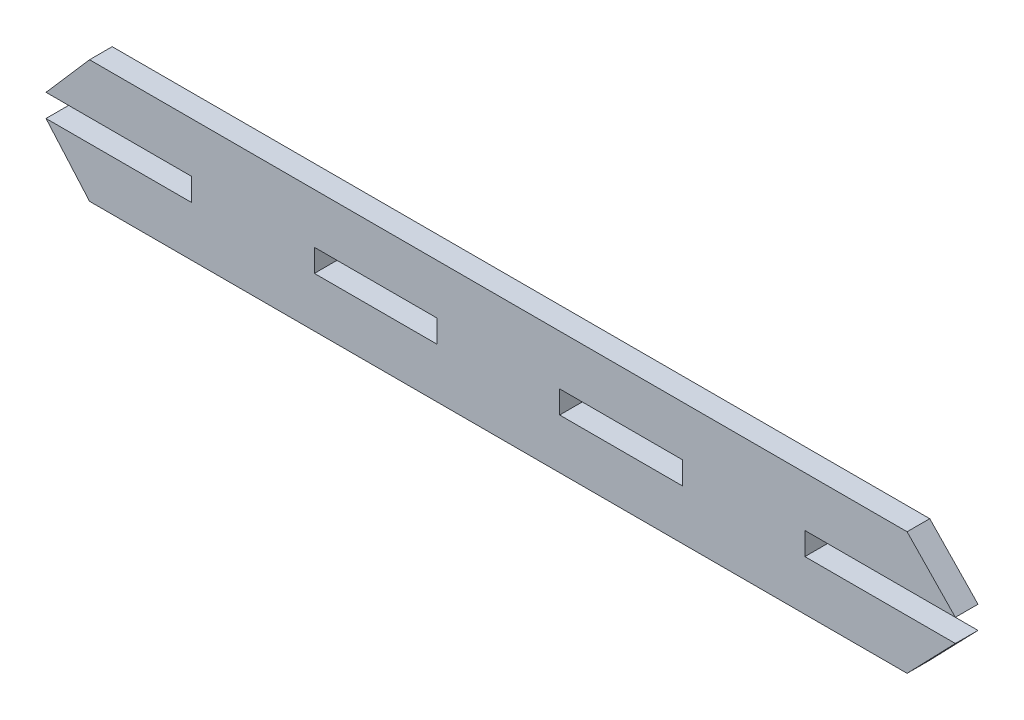
SolidWorks part; units mm, degrees
ref_plane "Front Plane" through (0, 0, 0) normal (0, 0, 1) x (1, 0, 0)
ref_plane "Top Plane" through (0, 0, 0) normal (0, 1, 0) x (1, 0, 0)
ref_plane "Right Plane" through (0, 0, 0) normal (1, 0, 0) x (0, 0, -1)
sketch "Sketch2" plane through (0, 0, 0) normal (0, 0, 1) x (1, 0, 0)
  line L5 (70.8837, 21.3653) -> (270.8837, 21.3653)
  line L35 (170.8837, 21.3653) -> (170.8837, 6.3653) construction
  line L40 (70.8837, -8.6347) -> (270.8837, -8.6347)
  line L42 (185.8837, 9.1353) -> (215.8837, 9.1353)
  line L43 (185.8837, 9.1353) -> (185.8837, 3.5953)
  line L44 (185.8837, 3.5953) -> (215.8837, 3.5953)
  line L45 (215.8837, 9.1353) -> (215.8837, 3.5953)
  line L57 (60.2283, 9.1353) -> (70.8837, 21.3653)
  line L58 (60.2283, 3.5953) -> (70.8837, -8.6347)
  line L59 (270.8837, -8.6347) -> (282.6872, 3.5953)
  line L60 (270.8837, 21.3653) -> (282.6872, 9.1353)
  line L62 (125.8837, 9.1353) -> (125.8837, 3.5953)
  line L63 (125.8837, 9.1353) -> (155.8837, 9.1353)
  line L64 (155.8837, 9.1353) -> (155.8837, 3.5953)
  line L65 (125.8837, 3.5953) -> (155.8837, 3.5953)
  line L67 (60.2283, 3.5953) -> (95.8837, 3.5953)
  line L69 (60.2283, 9.1353) -> (95.8837, 9.1353)
  line L70 (95.8837, 3.5953) -> (95.8837, 9.1353)
  line L71 (282.6872, 3.5953) -> (245.8837, 3.5953)
  line L73 (282.6872, 9.1353) -> (245.8837, 9.1353)
  line L74 (245.8837, 3.5953) -> (245.8837, 9.1353)
  point P12 (170.8837, 13.8653)
  dimension "D2" = 5.54
  dimension "D3" = 0
  dimension "D4" = 5.54
  dimension "D5" = 30
  dimension "D6" = 15
  dimension "D8" = 2
  dimension "D14" = 30
  dimension "D9" = 30
  dimension "D10" = 15
  dimension "D11" = 30
  dimension "D12" = 200
  dimension "D7" = 30
  dimension "D13" = 5.54
  dimension "D15" = 12.23
  dimension "D16" = 12.23
extrude "Boss-Extrude1" add sketch "Sketch2" along normal blind 5.54
